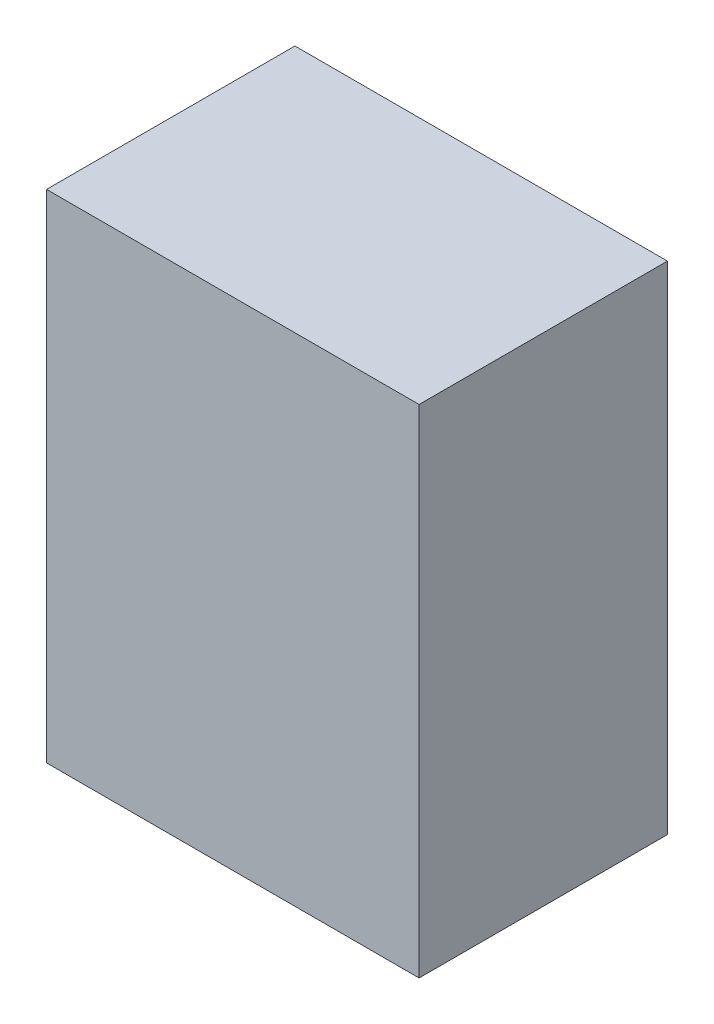
SolidWorks part; units mm, degrees
ref_plane "Front Plane" through (0, 0, 0) normal (0, 0, 1) x (1, 0, 0)
ref_plane "Top Plane" through (0, 0, 0) normal (0, 1, 0) x (1, 0, 0)
ref_plane "Right Plane" through (0, 0, 0) normal (1, 0, 0) x (0, 0, -1)
sketch "Sketch1" plane through (0, 0, 0) normal (0, 1, 0) x (1, 0, 0)
  line L1 (-2.3813, 1.5875) -> (2.3812, 1.5875)
  line L2 (-2.3813, 1.5875) -> (-2.3813, -1.5875)
  line L3 (-2.3813, -1.5875) -> (2.3812, -1.5875)
  line L4 (2.3812, 1.5875) -> (2.3812, -1.5875)
  line L5 (-2.3813, 1.5875) -> (2.3812, -1.5875) construction
  line L6 (-2.3813, -1.5875) -> (2.3812, 1.5875) construction
  point P0 (0, 0)
  dimension "D1" = 4.7625
  dimension "D2" = 3.175
extrude "Boss-Extrude1" add sketch "Sketch1" along normal blind 6.35
